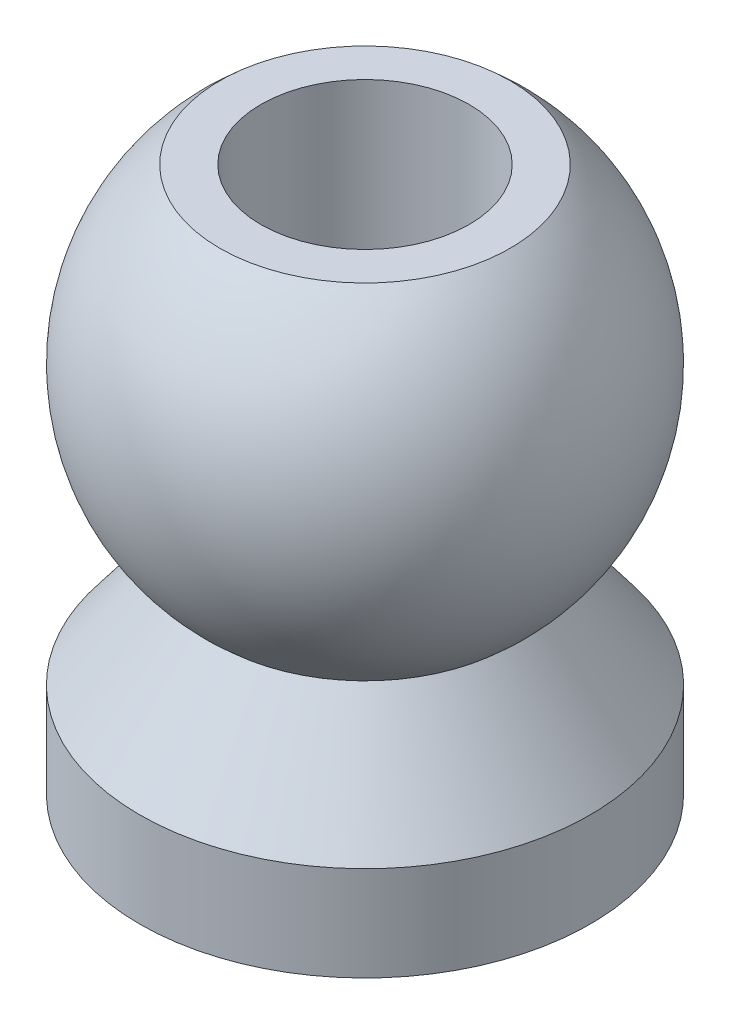
SolidWorks part; units mm, degrees
material "Brass"
ref_plane "Front Plane" through (0, 0, 0) normal (0, 0, 1) x (1, 0, 0)
ref_plane "Top Plane" through (0, 0, 0) normal (0, 1, 0) x (1, 0, 0)
ref_plane "Right Plane" through (0, 0, 0) normal (1, 0, 0) x (0, 0, -1)
sketch "Sketch2" plane through (0, 0, 0) normal (0, 0, 1) x (1, 0, 0)
  line L0 (0, 4.3805) -> (0, -5.41) construction
  line L1 (-1.1, -3.94) -> (-2.38, -3.94)
  line L2 (-2.38, -3.94) -> (-2.38, -2.94)
  line L3 (-2.38, -2.94) -> (-1.5336, -1.82)
  line L5 (-1.5336, -1.82) -> (0, -1.82) construction
  line L6 (-1.1, 1.82) -> (-1.5336, 1.82)
  line L8 (-1.1, 1.82) -> (-1.1, -3.94)
  circle A0 centre (0, 0) radius 2.38 construction
  arc A1 (-1.5336, 1.82) -> (-1.5336, -1.82) centre (0, 0) ccw
  dimension "D1" = 4.76
  dimension "D2" = 3.64
  dimension "D3" = 2.12
  dimension "D4" = 2.38
  dimension "D5" = 1.1
  dimension "D6" = 1
revolve "Ball Link" add sketch "Sketch2" angle 360 about L0
